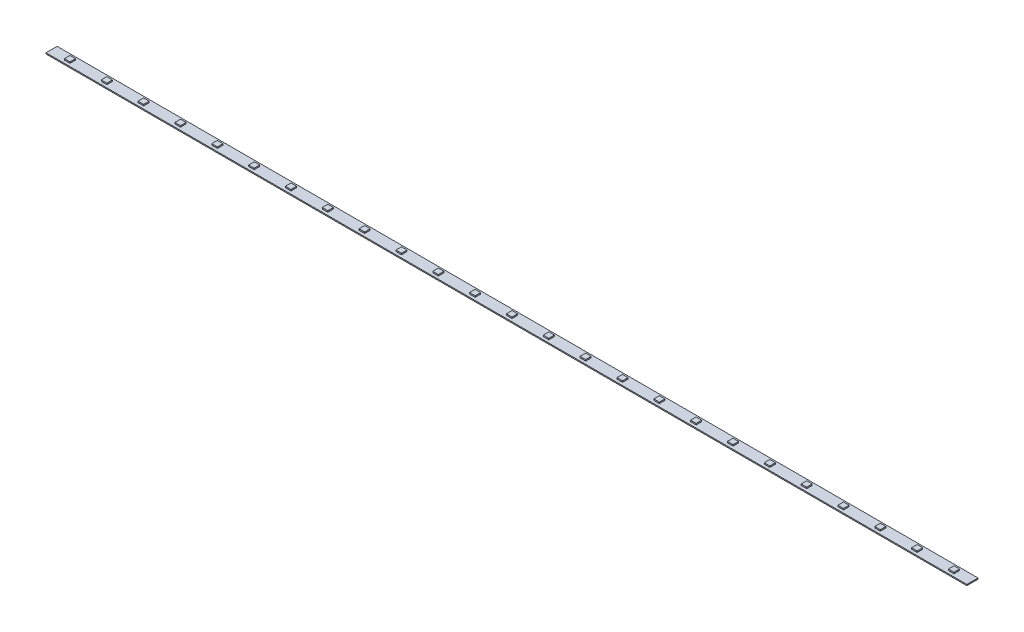
SolidWorks part; units mm, degrees
ref_plane "Ebene vorne" through (0, 0, 0) normal (0, 0, 1) x (1, 0, 0)
ref_plane "Ebene oben" through (0, 0, 0) normal (0, 1, 0) x (1, 0, 0)
ref_plane "Ebene rechts" through (0, 0, 0) normal (1, 0, 0) x (0, 0, -1)
sketch "Sketch1" plane through (0, 0, 0) normal (0, 1, 0) x (1, 0, 0)
  line L1 (-16.5, -5) -> (16.5, -5)
  line L2 (-16.5, -5) -> (-16.5, 5)
  line L3 (-16.5, 5) -> (16.5, 5)
  line L4 (16.5, -5) -> (16.5, 5)
  line L5 (-16.5, -5) -> (16.5, 5) construction
  line L6 (-16.5, 5) -> (16.5, -5) construction
  point P0 (0, 0)
  dimension "D1" = 33
  dimension "D2" = 10
extrude "Boss-Extrude1" add sketch "Sketch1" along normal blind 1
sketch "Sketch3" plane through (0, 1, 0) normal (0, 1, 0) x (1, 0, 0)
  line L1 (-2.5, -2.5) -> (2.5, -2.5)
  line L2 (-2.5, -2.5) -> (-2.5, 2.5)
  line L3 (-2.5, 2.5) -> (2.5, 2.5)
  line L4 (2.5, -2.5) -> (2.5, 2.5)
  line L5 (-2.5, -2.5) -> (2.5, 2.5) construction
  line L6 (-2.5, 2.5) -> (2.5, -2.5) construction
  point P0 (0, 0)
  dimension "D1" = 5
  dimension "D2" = 5
extrude "Boss-Extrude2" add sketch "Sketch3" along normal blind 1.2
pattern_linear "LPattern1" count 13 spacing 33 along (-1, 0, 0) count 13 spacing 33 along (1, 0, 0) of "Boss-Extrude1", "Boss-Extrude2"
